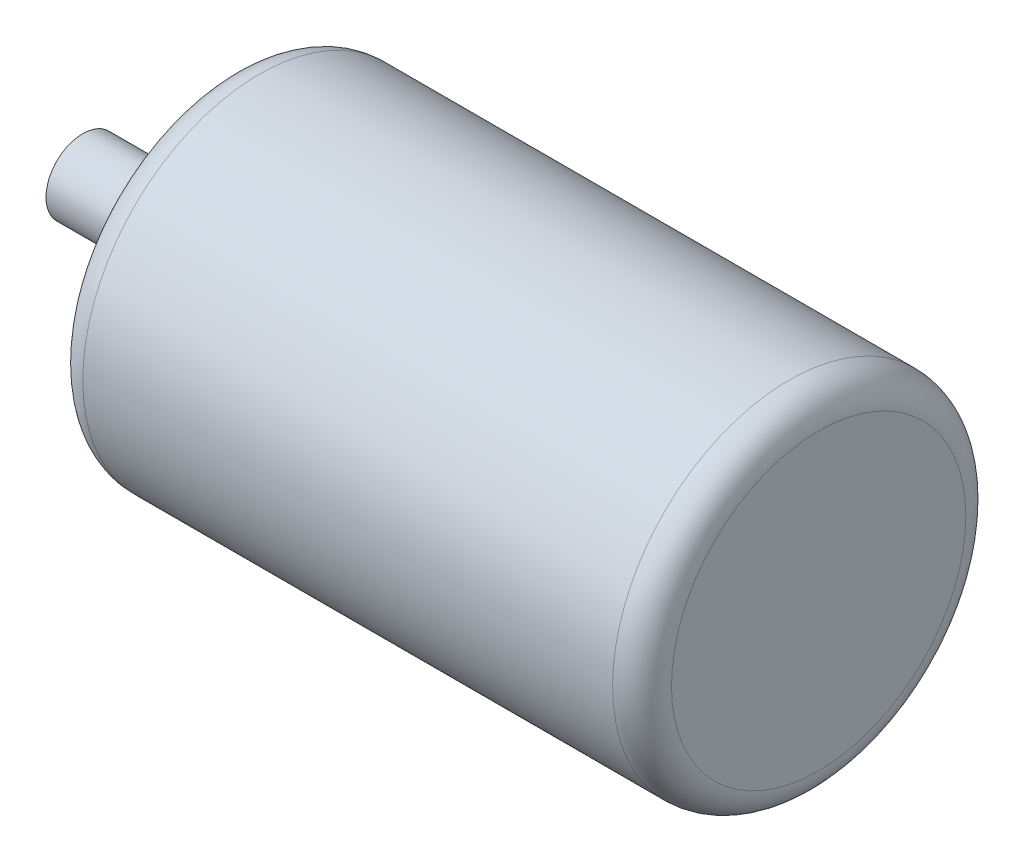
SolidWorks part; units mm, degrees
ref_plane "Front Plane" through (0, 0, 0) normal (0, 0, 1) x (1, 0, 0)
ref_plane "Top Plane" through (0, 0, 0) normal (0, 1, 0) x (1, 0, 0)
ref_plane "Right Plane" through (0, 0, 0) normal (1, 0, 0) x (0, 0, -1)
sketch "Sketch1" plane through (0, 0, 0) normal (1, 0, 0) x (0, 0, -1)
  circle A0 centre (0, 0) radius 60
  point P3 (0, 0)
  point P4 (0, 0)
extrude "Boss-Extrude1" add sketch "Sketch1" along normal blind 200 and the other way blind 50
sketch "Sketch2" plane through (-50, 0, 0) normal (-1, 0, 0) x (0, 0, 1)
  circle A0 centre (0, 0) radius 12.5
  circle A2 centre (0, 0) radius 75
extrude "Cut-Extrude1" cut sketch "Sketch2" against normal blind 50
fillet "Fillet1" radius 10 2 edges at (0, 0, 60) (200, 0, -60)
